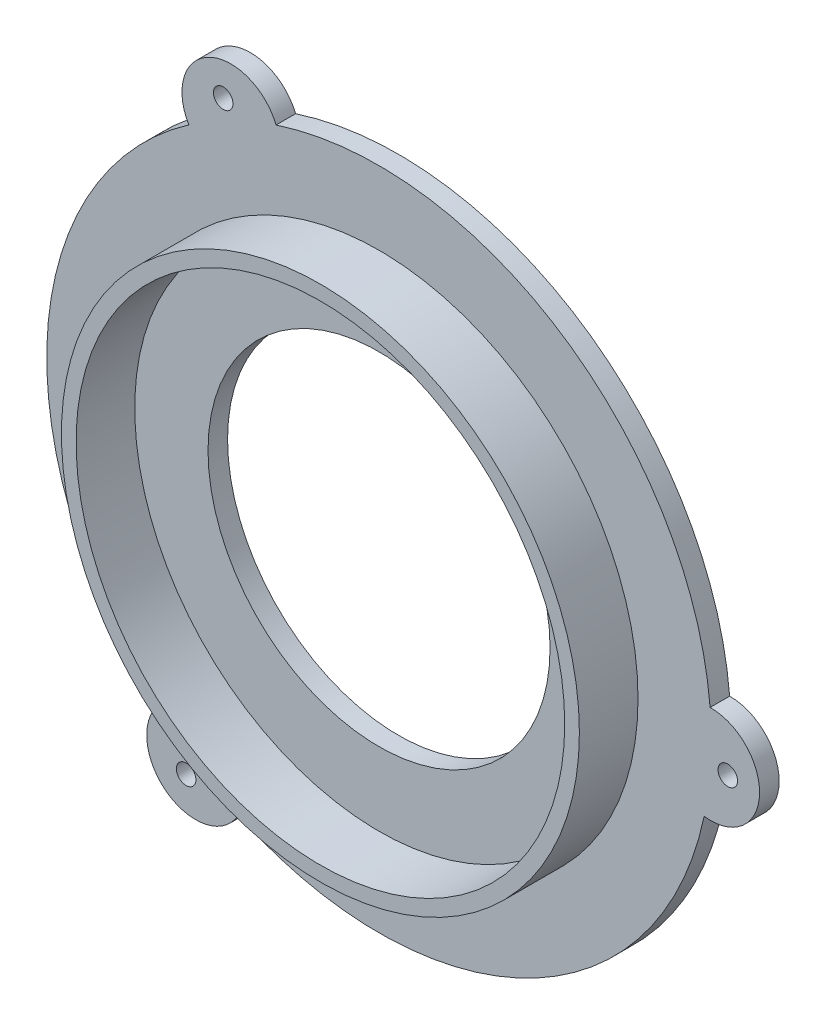
SolidWorks part; units mm, degrees
ref_plane "Front Plane" through (0, 0, 0) normal (0, 0, 1) x (1, 0, 0)
ref_plane "Top Plane" through (0, 0, 0) normal (0, 1, 0) x (1, 0, 0)
ref_plane "Right Plane" through (0, 0, 0) normal (1, 0, 0) x (0, 0, -1)
sketch "Sketch1" plane through (0, 0, 0) normal (0, 0, 1) x (1, 0, 0)
  line L0 (0, 0) -> (33.9362, -2.0821) construction
  line L2 (-31.1187, 23.5098) -> (-38.6046, 23.9691) construction
  line L3 (35.6829, -2.1893) -> (0, 0) construction
  arc A0 (-19.4639, 27.8775) -> (-22.7259, -25.289) centre (0, 0) ccw
  arc A3 (33.8746, 2.9175) -> (33.2639, -7.0367) centre (33.9362, -2.0821) cw
  arc A5 (-14.4107, -30.795) -> (-22.7259, -25.289) centre (-18.7713, -28.3485) cw
  arc A6 (-19.4639, 27.8775) -> (-10.5379, 32.3257) centre (-15.1649, 30.4307) cw
  arc A7 (-14.4107, -30.795) -> (33.2639, -7.0367) centre (0, 0) ccw
  arc A8 (33.8746, 2.9175) -> (-10.5379, 32.3257) centre (0, 0) ccw
  circle A10 centre (35.6829, -2.1893) radius 1
  circle A11 centre (-19.7375, -29.8076) radius 1
  circle A12 centre (-15.9455, 31.997) radius 1
  circle A13 centre (0, 0) radius 35.75 construction
  dimension "D1" = 68
  dimension "D2" = 5
  dimension "D3" = 3
  dimension "D4" = 2
  dimension "D5" = 1.75
  dimension "D6" = 3
extrude "Boss-Extrude1" add sketch "Sketch1" along normal blind 2
sketch "Sketch2" plane through (0, 0, 2) normal (0, 0, 1) x (1, 0, 0)
  circle A6 centre (0, 0) radius 25
  circle A7 centre (0, 0) radius 26.5
  dimension "D1" = 50
  dimension "D2" = 53
extrude "Boss-Extrude2" add sketch "Sketch2" along normal blind 6
sketch "Sketch3" plane through (0, 0, 2) normal (0, 0, 1) x (1, 0, 0)
  circle A0 centre (0, 0) radius 17.5
  dimension "D1" = 35
extrude "Cut-Extrude1" cut sketch "Sketch3" against normal blind 6
